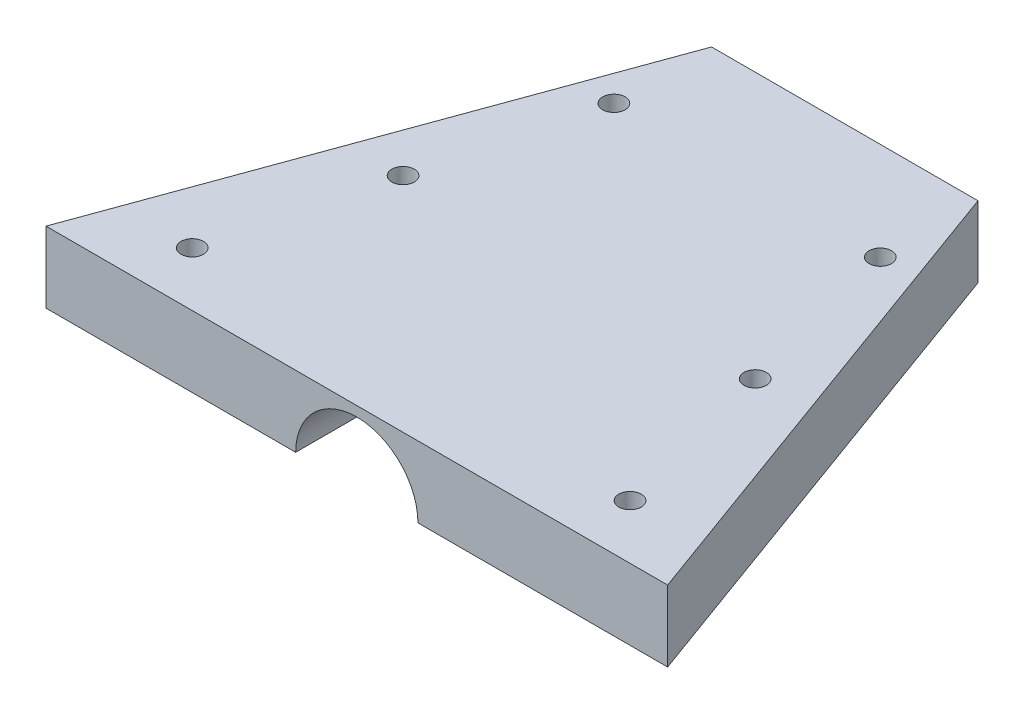
SolidWorks part; units mm, degrees
ref_plane "Front Plane" through (0, 0, 0) normal (0, 0, 1) x (1, 0, 0)
ref_plane "Top Plane" through (0, 0, 0) normal (0, 1, 0) x (1, 0, 0)
ref_plane "Right Plane" through (0, 0, 0) normal (1, 0, 0) x (0, 0, -1)
sketch "Sketch6" plane through (0, 0, 0) normal (0, 1, 0) x (1, 0, 0)
  line L0 (-16.8369, 5.7834) -> (13.1631, 5.7834)
  line L1 (13.1631, 5.7834) -> (33.1631, -49.1662)
  line L2 (33.1631, -49.1662) -> (-36.8369, -49.1662)
  line L3 (-36.8369, -49.1662) -> (-16.8369, 5.7834)
  circle A0 centre (13.1631, -5.2166) radius 1.78
  circle A1 centre (-16.8369, -5.2166) radius 1.78
  circle A2 centre (-26.4869, -43.0491) radius 1.78
  circle A3 centre (22.8131, -43.0491) radius 1.78
  dimension "D1" = 3.56
  dimension "D3" = 3.56
  dimension "D4" = 3.56
  dimension "D5" = 3.56
  dimension "D2" = 70
  dimension "D6" = 30
  dimension "D7" = 11
  dimension "D8" = 11
  dimension "D9" = 49.3
  dimension "D10" = 10.35
  dimension "D11" = 10.35
  dimension "D12" = 30
extrude "Boss-Extrude3" add sketch "Sketch6" along normal blind 8 contours L3 L0 L1 L2
sketch "Sketch8" plane through (0, 0, 49.1662) normal (0, 0, 1) x (1, 0, 0)
  line L0 (33.1631, 0) -> (-36.8369, 0) construction
  circle A0 centre (-1.8369, 0) radius 6.8846
extrude "Cut-Extrude3" cut sketch "Sketch8" against normal blind 88
sketch "Sketch9" plane through (0, 8, 0) normal (0, 1, 0) x (1, 0, 0)
  point P0 (-16.8369, -5.2166)
  point P1 (13.1631, -5.2166)
  point P3 (22.8131, -43.0491)
  point P5 (-26.4869, -43.0491)
  point P7 (17.9881, -24.1329)
  point P9 (-21.6619, -24.1329)
hole_wizard "#39 (0.0995) Diameter Hole1" positions "3DSketch2" profile "Sketch11" hole size "#39" standard "ANSI Inch" end condition through all
sketch3d "3DSketch2"
  point P0 (-16.8369, 0, 5.2166)
  point P3 (13.1631, 0, 5.2166)
  point P6 (22.8131, 0, 43.0491)
  point P9 (-26.4869, 0, 43.0491)
  point P13 (22.8131, 8, 43.0491)
  point P16 (-26.4869, 8, 43.0491)
  point P19 (-16.8369, 8, 5.2166)
  point P22 (13.1631, 8, 5.2166)
  point P25 (-21.6619, 8, 24.1329)
  point P28 (17.9881, 8, 24.1329)
sketch "Sketch11" plane through (17.9881, 8, 24.1329) normal (1, 0, 0) x (0, 0, 1)
  line L0 (0, 0) -> (0, 8)
  line L1 (0, 8) -> (1.2636, 8)
  line L2 (1.2636, 8) -> (1.2636, 0)
  line L5 (1.2636, 0) -> (0, 0)
  line L11 (0, -6.35) -> (0, 107.95) construction
  dimension "Thru Hole Dia." = 2.5273
  dimension "Thru Hole Depth" = 8
